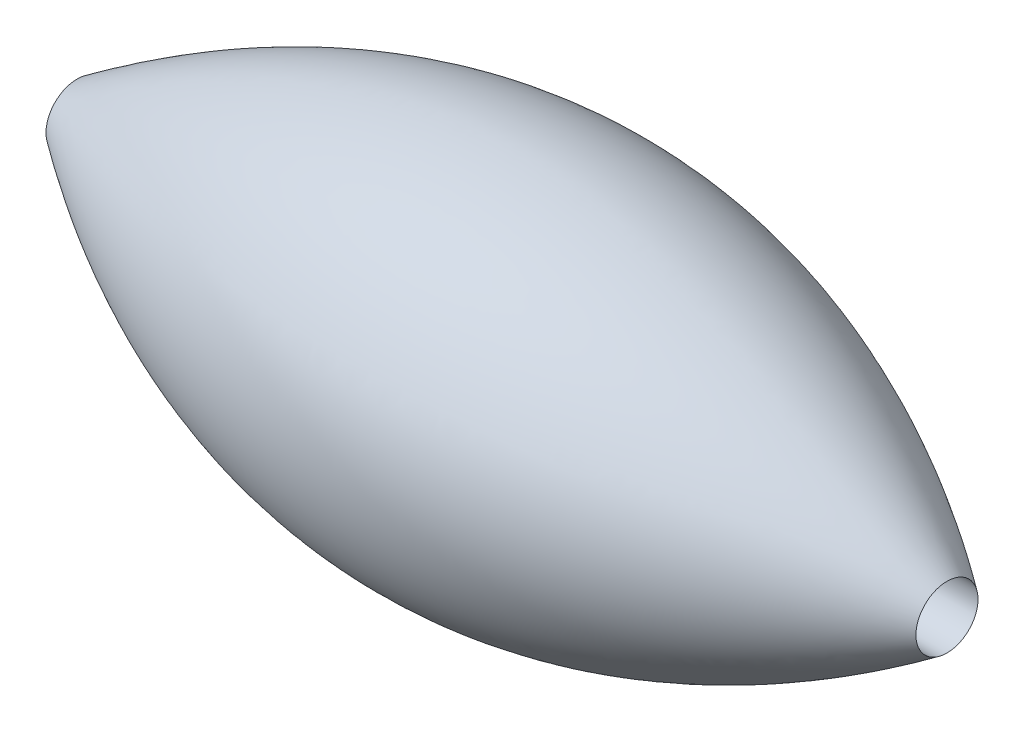
SolidWorks part; units mm, degrees
ref_plane "Front Plane" through (0, 0, 0) normal (0, 0, 1) x (1, 0, 0)
ref_plane "Top Plane" through (0, 0, 0) normal (0, 1, 0) x (1, 0, 0)
ref_plane "Right Plane" through (0, 0, 0) normal (1, 0, 0) x (0, 0, -1)
sketch "Sketch1" plane through (0, 0, 0) normal (0, 0, 1) x (1, 0, 0)
  line L0 (0, 0) -> (28, 0)
  line L1 (14, 0) -> (14, 5) construction
  line L3 (0, 0) -> (28, 0)
  line L4 (0, 0) -> (0, -1)
  line L5 (0, -1) -> (28, -1)
  line L6 (28, 0) -> (28, -1)
  spline S0 degree 2 poles (0, 0) (14, 10) (28, 0) knots 0 0 0 1 1 1
  dimension "D1" = 28
  dimension "D2" = 5
  dimension "D3" = 1
revolve "Revolve1" add sketch "Sketch1" angle 360 about L5
